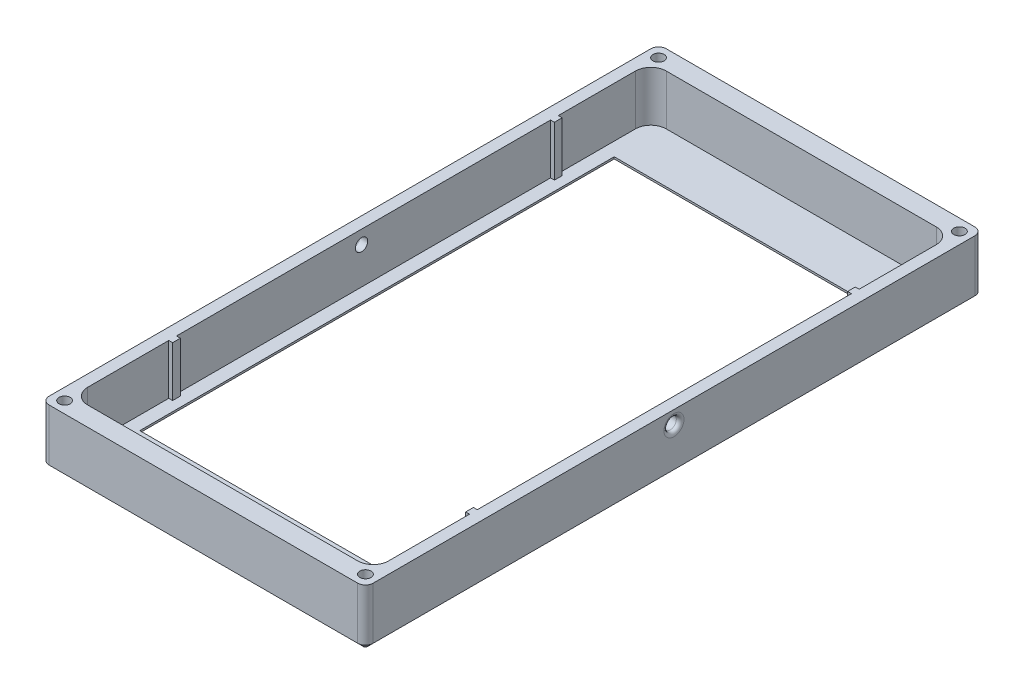
SolidWorks part; units mm, degrees
ref_plane "前视基准面" through (0, 0, 0) normal (0, 0, 1) x (1, 0, 0)
ref_plane "上视基准面" through (0, 0, 0) normal (0, 1, 0) x (1, 0, 0)
ref_plane "右视基准面" through (0, 0, 0) normal (1, 0, 0) x (0, 0, -1)
sketch "草图3" plane through (0, 0, 0) normal (0, 1, 0) x (1, 0, 0)
  line L0 (0, 1432.1227) -> (78, 1432.1227) construction
  line L1 (0, 1423.1618) -> (78, 1423.1618) construction
  line L2 (0, 1348.1618) -> (19, 1348.1618)
  line L3 (0, 1348.1618) -> (0, 1498.1618)
  line L4 (0, 1498.1618) -> (19, 1498.1618)
  line L5 (78, 1348.1618) -> (78, 1498.1618)
  line L6 (39, 1498.1618) -> (39, 1348.1618) construction
  line L7 (19, 1498.1618) -> (29, 1518.1618)
  line L8 (29, 1518.1618) -> (49, 1518.1618)
  line L9 (49, 1518.1618) -> (59, 1498.1618)
  line L10 (49, 1328.1618) -> (59, 1348.1618)
  line L11 (29, 1328.1618) -> (49, 1328.1618)
  line L12 (19, 1348.1618) -> (29, 1328.1618)
  line L13 (59, 1348.1618) -> (78, 1348.1618)
  line L14 (59, 1498.1618) -> (78, 1498.1618)
  line L15 (-3, 1345.1618) -> (17.1459, 1345.1618)
  line L16 (17.1459, 1345.1618) -> (27.1459, 1325.1618)
  line L17 (27.1459, 1325.1618) -> (50.8541, 1325.1618)
  line L18 (50.8541, 1325.1618) -> (60.8541, 1345.1618)
  line L19 (60.8541, 1345.1618) -> (81, 1345.1618)
  line L20 (81, 1345.1618) -> (81, 1501.1618)
  line L21 (60.8541, 1501.1618) -> (81, 1501.1618)
  line L22 (50.8541, 1521.1618) -> (60.8541, 1501.1618)
  line L23 (27.1459, 1521.1618) -> (50.8541, 1521.1618)
  line L24 (17.1459, 1501.1618) -> (27.1459, 1521.1618)
  line L25 (-3, 1501.1618) -> (17.1459, 1501.1618)
  line L26 (-3, 1345.1618) -> (-3, 1501.1618)
  line L27 (0, 1420.1618) -> (78, 1420.1618)
  line L28 (36, 1498.1618) -> (36, 1348.1618)
  dimension "D1" = 78
  dimension "D2" = 78
  dimension "D3" = 150
  dimension "D4" = 20
  dimension "D5" = 20
  dimension "D6" = 20
  dimension "D7" = 20
  dimension "D8" = 10
extrude "凸台-拉伸2" add sketch "草图3" along normal blind 15 contours L26 L15 L16 L17 L18 L19 L20 L21 L22 L23 L24 L25 L9 L14 L5 L13 L10 L11 L12 L2 L3 L4 L7 L8
fillet "圆角1" radius 2 8 edges at (60.8541, 7.5, -1501.1618) (17.1459, 7.5, -1501.1618) (19, 7.5, -1498.1618) (59, 7.5, -1498.1618) (29, 7.5, -1518.1618) (49, 7.5, -1518.1618) (50.8541, 7.5, -1521.1618) (27.1459, 7.5, -1521.1618)
fillet "圆角2" radius 2 8 edges at (59, 7.5, -1348.1618) (60.8541, 7.5, -1345.1618) (17.1459, 7.5, -1345.1618) (19, 7.5, -1348.1618) (29, 7.5, -1328.1618) (49, 7.5, -1328.1618) (50.8541, 7.5, -1325.1618) (27.1459, 7.5, -1325.1618)
fillet "圆角3" radius 4 4 edges at (81, 7.5, -1501.1618) (81, 7.5, -1345.1618) (-3, 7.5, -1345.1618) (-3, 7.5, -1501.1618)
fillet "圆角4" radius 4 4 edges at (0, 7.5, -1498.1618) (0, 7.5, -1348.1618) (78, 7.5, -1348.1618) (78, 7.5, -1498.1618)
sketch "草图4" plane through (0, 15, 0) normal (0, 1, 0) x (1, 0, 0)
  line L0 (8.4549, 1345.1618) -> (22.1459, 1335.1618)
  line L1 (1, 1345.1618) -> (15.9098, 1345.1618) construction
  line L2 (17.6987, 1344.0562) -> (26.5931, 1326.2674) construction
  line L3 (17.6987, 1344.0562) -> (22.1459, 1335.1618)
  line L4 (8.4549, 1345.1618) -> (15.9098, 1345.1618)
  line L5 (0, 1423.1618) -> (78, 1423.1618) construction
  line L6 (0, 1352.1618) -> (0, 1494.1618) construction
  line L7 (78, 1352.1618) -> (78, 1494.1618) construction
  line L8 (39, 1328.1618) -> (39, 1518.1618) construction
  line L9 (30.2361, 1328.1618) -> (47.7639, 1328.1618) construction
  line L10 (30.2361, 1518.1618) -> (47.7639, 1518.1618) construction
  line L11 (69.5451, 1345.1618) -> (62.0902, 1345.1618)
  line L12 (60.3013, 1344.0562) -> (55.8541, 1335.1618)
  line L13 (69.5451, 1345.1618) -> (55.8541, 1335.1618)
  line L14 (69.5451, 1501.1618) -> (55.8541, 1511.1618)
  line L15 (60.3013, 1502.2674) -> (55.8541, 1511.1618)
  line L16 (69.5451, 1501.1618) -> (62.0902, 1501.1618)
  line L17 (8.4549, 1501.1618) -> (15.9098, 1501.1618)
  line L18 (17.6987, 1502.2674) -> (22.1459, 1511.1618)
  line L19 (8.4549, 1501.1618) -> (22.1459, 1511.1618)
  arc A0 (17.6987, 1344.0562) -> (15.9098, 1345.1618) centre (15.9098, 1343.1618) ccw construction
  arc A1 (17.6987, 1344.0562) -> (15.9098, 1345.1618) centre (15.9098, 1343.1618) ccw
  arc A2 (60.3013, 1344.0562) -> (62.0902, 1345.1618) centre (62.0902, 1343.1618) cw
  arc A3 (60.3013, 1502.2674) -> (62.0902, 1501.1618) centre (62.0902, 1503.1618) ccw
  arc A4 (17.6987, 1502.2674) -> (15.9098, 1501.1618) centre (15.9098, 1503.1618) cw
extrude "凸台-拉伸3" add sketch "草图4" against normal up to surface (15 mm away) up to face at (39, 0, -1423.1618)
fillet "圆角5" radius 2 8 edges at (8.4549, 7.5, -1501.1618) (22.1459, 7.5, -1511.1618) (55.8541, 7.5, -1511.1618) (69.5451, 7.5, -1501.1618) (55.8541, 7.5, -1335.1618) (69.5451, 7.5, -1345.1618) (22.1459, 7.5, -1335.1618) (8.4549, 7.5, -1345.1618)
sketch "草图5" plane through (0, 15, 0) normal (0, 1, 0) x (1, 0, 0)
  line L0 (0, 1352.1618) -> (0, 1494.1618) construction
  line L1 (4, 1348.1618) -> (17.7639, 1348.1618) construction
  line L2 (0, 1423.1618) -> (78, 1423.1618) construction
  line L3 (78, 1352.1618) -> (78, 1494.1618) construction
  line L4 (39, 1325.1618) -> (39, 1521.1618) construction
  line L7 (28.382, 1325.1618) -> (49.618, 1325.1618) construction
  line L8 (28.382, 1521.1618) -> (49.618, 1521.1618) construction
  circle A0 centre (16, 1344.6618) radius 1.45
  circle A2 centre (62, 1344.6618) radius 1.45
  circle A3 centre (62, 1501.6618) radius 1.45
  circle A4 centre (16, 1501.6618) radius 1.45
  dimension "D1" = 2.9
  dimension "D2" = 16
  dimension "D3" = 3.5
extrude "切除-拉伸1" cut sketch "草图5" against normal blind 10
sketch "草图6" plane through (0, 0, 0) normal (0, -1, 0) x (1, 0, 0)
  line L0 (70.1977, -1501.1618) -> (77, -1501.1618) construction
  line L1 (69.0181, -1501.5467) -> (56.2462, -1510.8754) construction
  line L2 (51.4069, -1520.0562) -> (55.637, -1511.5961) construction
  line L3 (28.382, -1521.1618) -> (49.618, -1521.1618) construction
  line L4 (22.363, -1511.5961) -> (26.5931, -1520.0562) construction
  line L5 (21.7538, -1510.8754) -> (8.9819, -1501.5467) construction
  line L6 (1, -1501.1618) -> (7.8023, -1501.1618) construction
  line L7 (70.1977, -1501.1618) -> (77, -1501.1618)
  line L8 (69.0181, -1501.5467) -> (56.2462, -1510.8754)
  line L9 (51.4069, -1520.0562) -> (55.637, -1511.5961)
  line L10 (28.382, -1521.1618) -> (49.618, -1521.1618)
  line L11 (22.363, -1511.5961) -> (26.5931, -1520.0562)
  line L12 (21.7538, -1510.8754) -> (8.9819, -1501.5467)
  line L13 (1, -1501.1618) -> (7.8023, -1501.1618)
  line L14 (-3, -1497.1618) -> (-3, -1487.1618)
  line L15 (-3, -1349.1618) -> (-3, -1497.1618) construction
  line L16 (81, -1349.1618) -> (81, -1497.1618) construction
  line L17 (81, -1497.1618) -> (81, -1487.1618)
  line L18 (81, -1423.1618) -> (-3, -1423.1618) construction
  line L19 (81, -1349.1618) -> (81, -1359.1618)
  line L20 (-3, -1349.1618) -> (-3, -1359.1618)
  line L21 (1, -1345.1618) -> (7.8023, -1345.1618)
  line L22 (21.7538, -1335.4482) -> (8.9819, -1344.7769)
  line L23 (22.363, -1334.7275) -> (26.5931, -1326.2674)
  line L24 (28.382, -1325.1618) -> (49.618, -1325.1618)
  line L25 (51.4069, -1326.2674) -> (55.637, -1334.7275)
  line L26 (69.0181, -1344.7769) -> (56.2462, -1335.4482)
  line L27 (70.1977, -1345.1618) -> (77, -1345.1618)
  line L28 (-3, -1487.1618) -> (81, -1487.1618)
  line L29 (-3, -1359.1618) -> (81, -1359.1618)
  arc A0 (77, -1501.1618) -> (81, -1497.1618) centre (77, -1497.1618) ccw construction
  arc A1 (70.1977, -1501.1618) -> (69.0181, -1501.5467) centre (70.1977, -1503.1618) ccw construction
  arc A2 (56.2462, -1510.8754) -> (55.637, -1511.5961) centre (57.4258, -1512.4905) ccw construction
  arc A3 (49.618, -1521.1618) -> (51.4069, -1520.0562) centre (49.618, -1519.1618) ccw construction
  arc A4 (26.5931, -1520.0562) -> (28.382, -1521.1618) centre (28.382, -1519.1618) ccw construction
  arc A5 (22.363, -1511.5961) -> (21.7538, -1510.8754) centre (20.5742, -1512.4905) ccw construction
  arc A6 (8.9819, -1501.5467) -> (7.8023, -1501.1618) centre (7.8023, -1503.1618) ccw construction
  arc A7 (-3, -1497.1618) -> (1, -1501.1618) centre (1, -1497.1618) ccw construction
  arc A8 (77, -1501.1618) -> (81, -1497.1618) centre (77, -1497.1618) ccw
  arc A9 (70.1977, -1501.1618) -> (69.0181, -1501.5467) centre (70.1977, -1503.1618) ccw
  arc A10 (56.2462, -1510.8754) -> (55.637, -1511.5961) centre (57.4258, -1512.4905) ccw
  arc A11 (49.618, -1521.1618) -> (51.4069, -1520.0562) centre (49.618, -1519.1618) ccw
  arc A12 (26.5931, -1520.0562) -> (28.382, -1521.1618) centre (28.382, -1519.1618) ccw
  arc A13 (22.363, -1511.5961) -> (21.7538, -1510.8754) centre (20.5742, -1512.4905) ccw
  arc A14 (8.9819, -1501.5467) -> (7.8023, -1501.1618) centre (7.8023, -1503.1618) ccw
  arc A15 (-3, -1497.1618) -> (1, -1501.1618) centre (1, -1497.1618) ccw
  arc A16 (-3, -1349.1618) -> (1, -1345.1618) centre (1, -1349.1618) cw
  arc A17 (8.9819, -1344.7769) -> (7.8023, -1345.1618) centre (7.8023, -1343.1618) cw
  arc A18 (22.363, -1334.7275) -> (21.7538, -1335.4482) centre (20.5742, -1333.8331) cw
  arc A19 (26.5931, -1326.2674) -> (28.382, -1325.1618) centre (28.382, -1327.1618) cw
  arc A20 (49.618, -1325.1618) -> (51.4069, -1326.2674) centre (49.618, -1327.1618) cw
  arc A21 (56.2462, -1335.4482) -> (55.637, -1334.7275) centre (57.4258, -1333.8331) cw
  arc A22 (70.1977, -1345.1618) -> (69.0181, -1344.7769) centre (70.1977, -1343.1618) cw
  arc A23 (77, -1345.1618) -> (81, -1349.1618) centre (77, -1349.1618) cw
  dimension "D1" = 10
  dimension "D2" = 10
extrude "凸台-拉伸4" add sketch "草图6" against normal blind 2
sketch "草图7" plane through (0, 0, 0) normal (0, -1, 0) x (1, 0, 0)
  line L0 (-181.754, -1616.3229) -> (-181.754, -1300.3229) construction
  line L1 (40.0872, -1542.3284) -> (38.71, -1522.3759) construction
  line L2 (47.0207, -1512.0978) -> (47.0207, -1506.6644)
  line L3 (47.0207, -1506.6644) -> (27.0207, -1494.6574)
  line L4 (27.0207, -1494.6574) -> (27.0207, -1500.6574)
  line L5 (27.0207, -1500.6574) -> (46.7827, -1512.5215)
  line L6 (46.7827, -1512.5215) -> (47.0207, -1512.0978)
  line L7 (47.0207, -1502.4044) -> (47.0207, -1497.1653)
  line L8 (47.0207, -1497.1653) -> (37.0207, -1491.1618)
  line L9 (37.0207, -1491.1618) -> (37.0207, -1497.1618)
  line L10 (37.0207, -1497.1618) -> (47.0207, -1503.1653)
  line L11 (47.0207, -1503.1653) -> (47.0207, -1502.4044)
  line L17 (37.0207, -1510.16) -> (37.0207, -1516.16)
  line L18 (37.0207, -1516.16) -> (27.0207, -1510.1565)
  line L19 (27.0207, -1510.1565) -> (27.0207, -1504.1565)
  line L20 (27.0207, -1504.1565) -> (37.0207, -1510.16)
  line L22 (78, -1487.1618) -> (0, -1487.1618) construction
  line L23 (0, -1423.1618) -> (78, -1423.1618) construction
  line L24 (0, -1359.1618) -> (0, -1487.1618) construction
  line L25 (78, -1359.1618) -> (78, -1487.1618) construction
  line L26 (47.0207, -1343.1653) -> (47.0207, -1342.4044)
  line L27 (47.0207, -1342.4044) -> (47.0207, -1337.1653)
  line L28 (47.0207, -1337.1653) -> (37.0207, -1331.1618)
  line L29 (37.0207, -1331.1618) -> (37.0207, -1337.1618)
  line L30 (37.0207, -1337.1618) -> (47.0207, -1343.1653)
  line L31 (46.7827, -1352.5215) -> (47.0207, -1352.0978)
  line L32 (47.0207, -1352.0978) -> (47.0207, -1346.6644)
  line L33 (47.0207, -1346.6644) -> (27.0207, -1334.6574)
  line L34 (27.0207, -1334.6574) -> (27.0207, -1340.6574)
  line L35 (27.0207, -1340.6574) -> (46.7827, -1352.5215)
  line L36 (27.0207, -1344.1565) -> (37.0207, -1350.16)
  line L37 (37.0207, -1350.16) -> (37.0207, -1356.16)
  line L38 (37.0207, -1356.16) -> (27.0207, -1350.1565)
  line L39 (27.0207, -1350.1565) -> (27.0207, -1344.1565)
  dimension "D1" = 20
  dimension "D2" = 6
  dimension "D3" = 6
  dimension "D4" = 3
  dimension "D5" = 20
  dimension "D6" = 10
  dimension "D7" = 6
  dimension "D8" = 0
  dimension "D9" = 3
  dimension "D10" = 4
  dimension "D11" = 2
sketch "草图8" plane through (0, 2, 0) normal (0, 1, 0) x (1, 0, 0)
  line L0 (220.2617, 2782.0632) -> (1100.2617, 2782.0632) construction
  line L17 (26.5931, 1520.0562) -> (22.363, 1511.5961)
  line L18 (21.7538, 1510.8754) -> (8.9819, 1501.5467)
  line L19 (7.8023, 1501.1618) -> (1, 1501.1618)
  line L20 (-3, 1497.1618) -> (-3, 1349.1618)
  line L21 (1, 1345.1618) -> (7.8023, 1345.1618)
  line L22 (8.9819, 1344.7769) -> (21.7538, 1335.4482)
  line L23 (22.363, 1334.7275) -> (26.5931, 1326.2674)
  line L24 (28.382, 1325.1618) -> (49.618, 1325.1618)
  line L25 (51.4069, 1326.2674) -> (55.637, 1334.7275)
  line L26 (56.2462, 1335.4482) -> (69.0181, 1344.7769)
  line L27 (70.1977, 1345.1618) -> (77, 1345.1618)
  line L28 (81, 1349.1618) -> (81, 1497.1618)
  line L29 (77, 1501.1618) -> (70.1977, 1501.1618)
  line L30 (69.0181, 1501.5467) -> (56.2462, 1510.8754)
  line L31 (55.637, 1511.5961) -> (51.4069, 1520.0562)
  line L32 (49.618, 1521.1618) -> (28.382, 1521.1618)
  line L33 (26.5931, 1520.0562) -> (22.363, 1511.5961)
  line L34 (21.7538, 1510.8754) -> (8.9819, 1501.5467)
  line L35 (7.8023, 1501.1618) -> (1, 1501.1618)
  line L36 (-3, 1497.1618) -> (-3, 1349.1618)
  line L37 (1, 1345.1618) -> (7.8023, 1345.1618)
  line L38 (8.9819, 1344.7769) -> (21.7538, 1335.4482)
  line L39 (22.363, 1334.7275) -> (26.5931, 1326.2674)
  line L40 (28.382, 1325.1618) -> (49.618, 1325.1618)
  line L41 (51.4069, 1326.2674) -> (55.637, 1334.7275)
  line L42 (56.2462, 1335.4482) -> (69.0181, 1344.7769)
  line L43 (70.1977, 1345.1618) -> (77, 1345.1618)
  line L44 (81, 1349.1618) -> (81, 1497.1618)
  line L45 (77, 1501.1618) -> (70.1977, 1501.1618)
  line L46 (69.0181, 1501.5467) -> (56.2462, 1510.8754)
  line L47 (55.637, 1511.5961) -> (51.4069, 1520.0562)
  line L48 (49.618, 1521.1618) -> (28.382, 1521.1618)
  arc A16 (21.7538, 1510.8754) -> (22.363, 1511.5961) centre (20.5742, 1512.4905) ccw
  arc A17 (7.8023, 1501.1618) -> (8.9819, 1501.5467) centre (7.8023, 1503.1618) ccw
  arc A18 (1, 1501.1618) -> (-3, 1497.1618) centre (1, 1497.1618) ccw
  arc A19 (-3, 1349.1618) -> (1, 1345.1618) centre (1, 1349.1618) ccw
  arc A20 (8.9819, 1344.7769) -> (7.8023, 1345.1618) centre (7.8023, 1343.1618) ccw
  arc A21 (22.363, 1334.7275) -> (21.7538, 1335.4482) centre (20.5742, 1333.8331) ccw
  arc A22 (26.5931, 1326.2674) -> (28.382, 1325.1618) centre (28.382, 1327.1618) ccw
  arc A23 (49.618, 1325.1618) -> (51.4069, 1326.2674) centre (49.618, 1327.1618) ccw
  arc A24 (56.2462, 1335.4482) -> (55.637, 1334.7275) centre (57.4258, 1333.8331) ccw
  arc A25 (70.1977, 1345.1618) -> (69.0181, 1344.7769) centre (70.1977, 1343.1618) ccw
  arc A26 (77, 1345.1618) -> (81, 1349.1618) centre (77, 1349.1618) ccw
  arc A27 (81, 1497.1618) -> (77, 1501.1618) centre (77, 1497.1618) ccw
  arc A28 (69.0181, 1501.5467) -> (70.1977, 1501.1618) centre (70.1977, 1503.1618) ccw
  arc A29 (55.637, 1511.5961) -> (56.2462, 1510.8754) centre (57.4258, 1512.4905) ccw
  arc A30 (51.4069, 1520.0562) -> (49.618, 1521.1618) centre (49.618, 1519.1618) ccw
  arc A31 (28.382, 1521.1618) -> (26.5931, 1520.0562) centre (28.382, 1519.1618) ccw
  arc A32 (21.7538, 1510.8754) -> (22.363, 1511.5961) centre (20.5742, 1512.4905) ccw
  arc A33 (7.8023, 1501.1618) -> (8.9819, 1501.5467) centre (7.8023, 1503.1618) ccw
  arc A34 (1, 1501.1618) -> (-3, 1497.1618) centre (1, 1497.1618) ccw
  arc A35 (-3, 1349.1618) -> (1, 1345.1618) centre (1, 1349.1618) ccw
  arc A36 (8.9819, 1344.7769) -> (7.8023, 1345.1618) centre (7.8023, 1343.1618) ccw
  arc A37 (22.363, 1334.7275) -> (21.7538, 1335.4482) centre (20.5742, 1333.8331) ccw
  arc A38 (26.5931, 1326.2674) -> (28.382, 1325.1618) centre (28.382, 1327.1618) ccw
  arc A39 (49.618, 1325.1618) -> (51.4069, 1326.2674) centre (49.618, 1327.1618) ccw
  arc A40 (56.2462, 1335.4482) -> (55.637, 1334.7275) centre (57.4258, 1333.8331) ccw
  arc A41 (70.1977, 1345.1618) -> (69.0181, 1344.7769) centre (70.1977, 1343.1618) ccw
  arc A42 (77, 1345.1618) -> (81, 1349.1618) centre (77, 1349.1618) ccw
  arc A43 (81, 1497.1618) -> (77, 1501.1618) centre (77, 1497.1618) ccw
  arc A44 (69.0181, 1501.5467) -> (70.1977, 1501.1618) centre (70.1977, 1503.1618) ccw
  arc A45 (55.637, 1511.5961) -> (56.2462, 1510.8754) centre (57.4258, 1512.4905) ccw
  arc A46 (51.4069, 1520.0562) -> (49.618, 1521.1618) centre (49.618, 1519.1618) ccw
  arc A47 (28.382, 1521.1618) -> (26.5931, 1520.0562) centre (28.382, 1519.1618) ccw
  dimension "D1" = 0
sketch "草图9" plane through (81, 0, 0) normal (1, 0, 0) x (0, 0, -1)
  line L0 (1349.1618, 15) -> (1497.1618, 15) construction
  circle A0 centre (1423.1618, 11.5) radius 1.6
  point P4 (1423.1618, 15)
  dimension "D1" = 3.2
  dimension "D2" = 3.5
extrude "切除-拉伸3" cut sketch "草图9" against normal up to surface (84 mm away) up to face at (-3, 7.5, -1423.1618)
fillet "圆角6" radius 1 2 edges at (-3, 11.5, -1421.5618) (81, 11.5, -1424.7618)
fillet "圆角7" radius 1 4 edges at (16, 15, -1343.2118) (62, 15, -1346.1118) (16, 15, -1503.1118) (62, 15, -1500.2118)
sketch "草图10" plane through (0, 0, 0) normal (0, -1, 0) x (1, 0, 0)
  line L0 (78, -1487.1618) -> (0, -1487.1618) construction
  line L1 (78, -1359.1618) -> (78, -1487.1618) construction
  line L2 (0, -1359.1618) -> (78, -1359.1618) construction
  line L3 (0, -1359.1618) -> (0, -1487.1618) construction
  line L4 (78, -1487.1618) -> (0, -1487.1618)
  line L5 (78, -1359.1618) -> (78, -1487.1618)
  line L6 (0, -1359.1618) -> (78, -1359.1618)
  line L7 (0, -1359.1618) -> (0, -1487.1618)
  line L8 (74.5, -1485.1618) -> (3.5, -1485.1618)
  line L9 (3.5, -1362.1618) -> (3.5, -1485.1618)
  line L10 (3.5, -1362.1618) -> (74.5, -1362.1618)
  line L11 (74.5, -1362.1618) -> (74.5, -1485.1618)
  dimension "D1" = 2
  dimension "D2" = 3.5
  dimension "D3" = 3.5
  dimension "D4" = 3
extrude "凸台-拉伸5" add sketch "草图10" against normal up to surface (2 mm away) up to face at (39, 2, -1344.472)
sketch "草图11" plane through (0, 2, 0) normal (0, 1, 0) x (1, 0, 0)
  line L0 (78, 1494.1618) -> (78, 1352.1618) construction
  line L1 (78, 1373.1618) -> (77, 1373.1618)
  line L2 (78, 1373.1618) -> (78, 1375.1618)
  line L3 (78, 1375.1618) -> (77, 1375.1618)
  line L4 (77, 1373.1618) -> (77, 1375.1618)
  line L5 (74.5, 1485.1618) -> (74.5, 1362.1618) construction
  line L6 (60.2361, 1348.1618) -> (74, 1348.1618) construction
  line L7 (39, 1362.1618) -> (39, 1485.1618) construction
  line L8 (74.5, 1362.1618) -> (3.5, 1362.1618) construction
  line L9 (3.5, 1485.1618) -> (74.5, 1485.1618) construction
  line L10 (74.5, 1423.6618) -> (3.5, 1423.6618) construction
  line L11 (3.5, 1362.1618) -> (3.5, 1485.1618) construction
  line L12 (1, 1373.1618) -> (1, 1375.1618)
  line L13 (0, 1375.1618) -> (1, 1375.1618)
  line L14 (0, 1373.1618) -> (0, 1375.1618)
  line L15 (0, 1373.1618) -> (1, 1373.1618)
  line L16 (0, 1474.1618) -> (1, 1474.1618)
  line L17 (0, 1474.1618) -> (0, 1472.1618)
  line L18 (0, 1472.1618) -> (1, 1472.1618)
  line L19 (1, 1474.1618) -> (1, 1472.1618)
  line L20 (77, 1474.1618) -> (77, 1472.1618)
  line L21 (78, 1472.1618) -> (77, 1472.1618)
  line L22 (78, 1474.1618) -> (78, 1472.1618)
  line L23 (78, 1474.1618) -> (77, 1474.1618)
  dimension "D1" = 2
  dimension "D2" = 25
  dimension "D3" = 1
extrude "凸台-拉伸6" add sketch "草图11" along normal up to surface (13 mm away) up to face at (16, 15, -1342.2118)
sketch "草图13" plane through (0, 15, 0) normal (0, 1, 0) x (1, 0, 0)
  circle A0 centre (62, 1501.6618) radius 2.45 construction
  circle A1 centre (16, 1501.6618) radius 2.45 construction
  circle A2 centre (62, 1344.6618) radius 2.45 construction
  circle A3 centre (16, 1344.6618) radius 2.45 construction
  circle A4 centre (62, 1501.6618) radius 2.45
  circle A5 centre (16, 1501.6618) radius 2.45
  circle A6 centre (62, 1344.6618) radius 2.45
  circle A7 centre (16, 1344.6618) radius 2.45
extrude "凸台-拉伸8" add sketch "草图13" against normal up to surface (13 mm away) up to face at (39, 2, -1423.6618)
sketch "草图14" plane through (0, 15, 0) normal (0, 1, 0) x (1, 0, 0)
  line L0 (7.8023, 1345.1618) -> (70.1977, 1345.1618)
  line L2 (70.1977, 1345.1618) -> (70.1977, 1307.3684)
  line L3 (70.1977, 1307.3684) -> (7.8023, 1307.3684)
  line L4 (7.8023, 1307.3684) -> (7.8023, 1345.1618)
  line L5 (-3, 1423.1618) -> (81, 1423.1618) construction
  line L6 (-3, 1349.1618) -> (-3, 1497.1618) construction
  line L7 (81, 1349.1618) -> (81, 1497.1618) construction
  line L8 (70.1977, 1538.9552) -> (7.8023, 1538.9552)
  line L9 (70.1977, 1501.1618) -> (70.1977, 1538.9552)
  line L10 (7.8023, 1501.1618) -> (70.1977, 1501.1618)
  line L11 (7.8023, 1538.9552) -> (7.8023, 1501.1618)
extrude "切除-拉伸4" cut sketch "草图14" against normal up to surface (15 mm away) up to face at (39, 0, -1423.1618)
sketch "草图15" plane through (0, 15, 0) normal (0, 1, 0) x (1, 0, 0)
  line L0 (-3, 1348.1618) -> (-3, 1343.1618)
  line L1 (-3, 1343.1618) -> (81, 1343.1618)
  line L2 (81, 1343.1618) -> (81, 1348.1618)
  line L3 (81, 1349.1618) -> (81, 1497.1618) construction
  line L4 (79.3028, 1348.1618) -> (-0.855, 1348.1618)
  line L5 (-3, 1349.1618) -> (-3, 1497.1618) construction
  line L7 (4, 1348.1618) -> (17.7639, 1348.1618) construction
  line L8 (-3, 1423.1618) -> (81, 1423.1618) construction
  line L13 (-3, 1348.1618) -> (-3, 1353.1618)
  line L14 (-3, 1353.1618) -> (-0.855, 1353.1618)
  line L15 (-0.855, 1353.1618) -> (-0.855, 1348.1618)
  line L16 (81, 1348.1618) -> (81, 1352.4013)
  line L17 (81, 1352.4013) -> (79.3028, 1352.4013)
  line L18 (79.3028, 1352.4013) -> (79.3028, 1348.1618)
  line L19 (79.3028, 1493.9223) -> (79.3028, 1498.1618)
  line L20 (81, 1493.9223) -> (79.3028, 1493.9223)
  line L21 (81, 1498.1618) -> (81, 1493.9223)
  line L22 (-0.855, 1493.1618) -> (-0.855, 1498.1618)
  line L23 (-3, 1493.1618) -> (-0.855, 1493.1618)
  line L24 (-3, 1498.1618) -> (-3, 1493.1618)
  line L25 (79.3028, 1498.1618) -> (-0.855, 1498.1618)
  line L26 (81, 1503.1618) -> (81, 1498.1618)
  line L27 (-3, 1503.1618) -> (81, 1503.1618)
  line L28 (-3, 1498.1618) -> (-3, 1503.1618)
  dimension "D1" = 0
  dimension "D2" = 5
  dimension "D3" = 5
extrude "凸台-拉伸9" add sketch "草图15" against normal up to surface (15 mm away) up to face at (39, 0, -1423.1618)
sketch "草图16" plane through (0, 15, 0) normal (0, 1, 0) x (1, 0, 0)
  line L0 (-3, 1343.1618) -> (-3, 1503.1618) construction
  line L1 (-3, 1343.1618) -> (81, 1343.1618) construction
  line L2 (-3, 1423.1618) -> (81, 1423.1618) construction
  line L3 (81, 1343.1618) -> (81, 1503.1618) construction
  line L4 (39, 1343.1618) -> (39, 1503.1618) construction
  line L5 (81, 1503.1618) -> (-3, 1503.1618) construction
  circle A0 centre (0, 1346.1618) radius 1.45
  circle A1 centre (0, 1500.1618) radius 1.45
  circle A2 centre (78, 1500.1618) radius 1.45
  circle A3 centre (78, 1346.1618) radius 1.45
  dimension "D1" = 2.9
  dimension "D2" = 3
  dimension "D3" = 3
extrude "切除-拉伸5" cut sketch "草图16" against normal up to surface (13 mm away) up to face at (39, 2, -1423.6618)
fillet "圆角8" radius 2 4 edges at (81, 7.5, -1503.1618) (-3, 7.5, -1503.1618) (-3, 7.5, -1343.1618) (81, 7.5, -1343.1618)
chamfer "倒角1" distance 1.5 angle 45 12 edges at (3.5, 0, -1423.6618) (39, 0, -1485.1618) (74.5, 0, -1423.6618) (39, 0, -1362.1618) (-2.4142, 0, -1502.576) (-3, 0, -1423.1618) (-2.4142, 0, -1343.7476) (39, 0, -1343.1618) (80.4142, 0, -1343.7476) (81, 0, -1423.1618) (80.4142, 0, -1502.576) (39, 0, -1503.1618)
